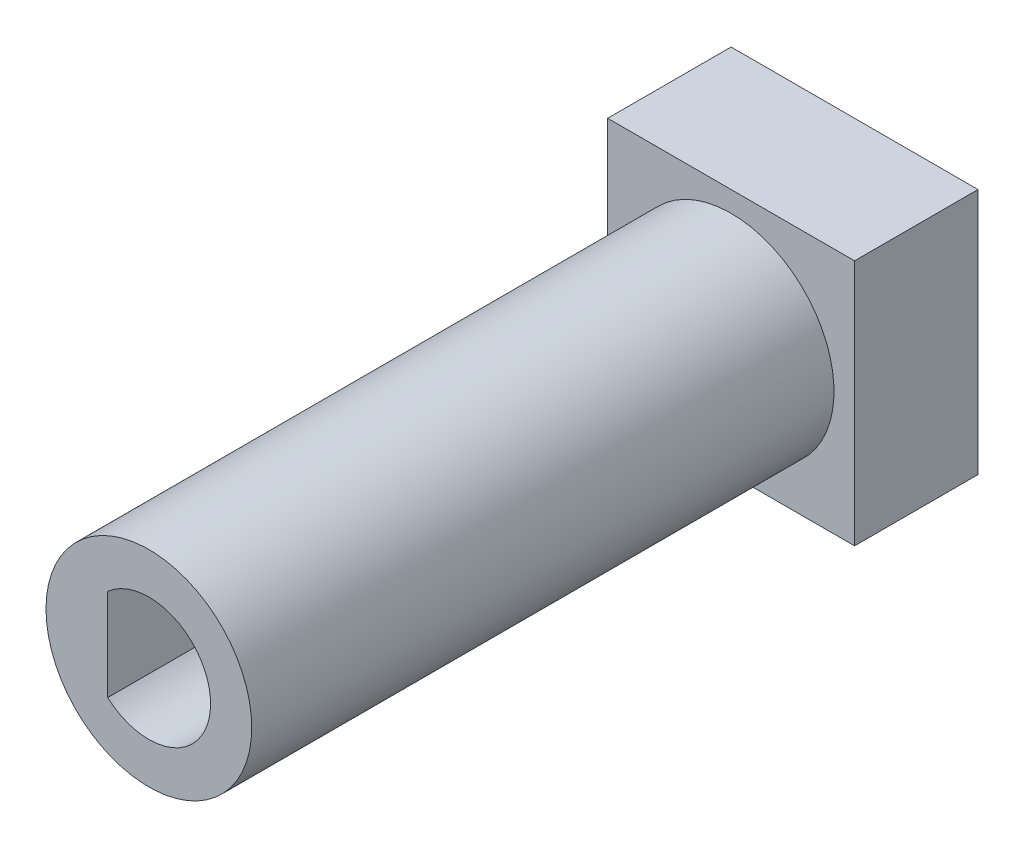
SolidWorks part; units mm, degrees
material "1023 Carbon Steel Sheet (SS)"
ref_plane "Front Plane" through (0, 0, 0) normal (0, 0, 1) x (1, 0, 0)
ref_plane "Top Plane" through (0, 0, 0) normal (0, 1, 0) x (1, 0, 0)
ref_plane "Right Plane" through (0, 0, 0) normal (1, 0, 0) x (0, 0, -1)
sketch "Sketch1" plane through (0, 0, 0) normal (0, 0, 1) x (1, 0, 0)
  line L1 (-6, -6) -> (6, -6)
  line L2 (-6, -6) -> (-6, 6)
  line L3 (-6, 6) -> (6, 6)
  line L4 (6, -6) -> (6, 6)
  line L5 (-6, -6) -> (6, 6) construction
  line L6 (-6, 6) -> (6, -6) construction
  point P0 (0, 0)
  dimension "D1" = 12
  dimension "D2" = 12
extrude "Boss-Extrude1" add sketch "Sketch1" along normal blind 6
sketch "Sketch2" plane through (0, 0, 6) normal (0, 0, 1) x (1, 0, 0)
  circle A0 centre (0, 0) radius 5
  dimension "D1" = 10
extrude "Boss-Extrude2" add sketch "Sketch2" along normal blind 10
sketch "Sketch3" plane through (0, 0, 16) normal (0, 0, 1) x (1, 0, 0)
  circle A0 centre (0, 0) radius 5
  dimension "D1" = 10
extrude "Boss-Extrude3" add sketch "Sketch3" along normal blind 18.3
sketch "Sketch5" plane through (0, 0, 34.3) normal (0, 0, 1) x (1, 0, 0)
  line L0 (-2, 2.2361) -> (-2, -2.2361)
  arc A0 (-2, -2.2361) -> (-2, 2.2361) centre (0, 0) ccw
  dimension "D1" = 6
  dimension "D2" = 2
extrude "Cut-Extrude2" cut sketch "Sketch5" against normal blind 22
sketch "Sketch6" plane through (0, 0, 0) normal (0, 0, -1) x (-1, 0, 0)
  circle A0 centre (0, 0) radius 4
  dimension "D1" = 8
extrude "Cut-Extrude3" cut sketch "Sketch6" against normal blind 6
